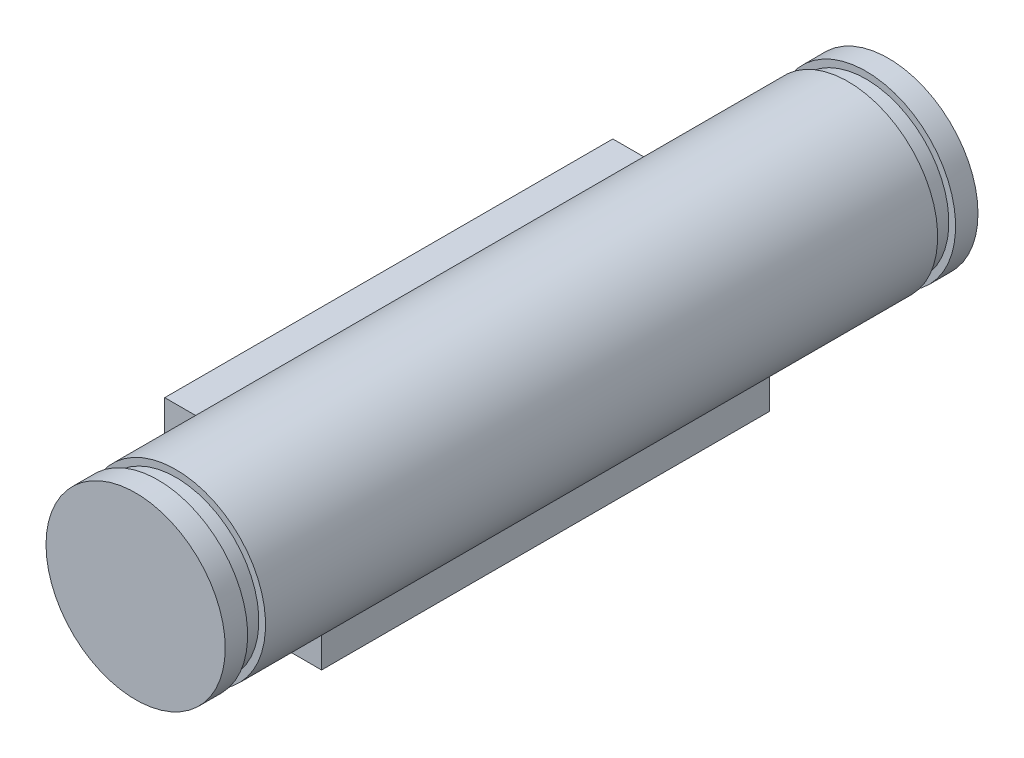
SolidWorks part; units mm, degrees
ref_plane "前视基准面" through (0, 0, 0) normal (0, 0, 1) x (1, 0, 0)
ref_plane "上视基准面" through (0, 0, 0) normal (0, 1, 0) x (1, 0, 0)
ref_plane "右视基准面" through (0, 0, 0) normal (1, 0, 0) x (0, 0, -1)
sketch "草图1" plane through (0, 0, 0) normal (0, 0, 1) x (1, 0, 0)
  line L0 (0, 7.5) -> (0, -7.5) construction
  line L1 (-7.5, -7.5) -> (7.5, -7.5)
  line L2 (-7.5, 7.5) -> (-7.5, -7.5)
  line L3 (-7.5, 7.5) -> (7.5, 7.5)
  line L4 (7.5, -7.5) -> (7.5, 7.5)
  line L5 (7.5, 0) -> (-7.5, 0) construction
  circle A0 centre (0, 0) radius 4
  circle A1 centre (-5, 5) radius 1.5
  circle A2 centre (-5, -5) radius 1.5
  circle A3 centre (5, -5) radius 1.5
  circle A4 centre (5, 5) radius 1.5
extrude "凸台-拉伸1" add sketch "草图1" along normal mid plane 33.6 contours A0
sketch "草图2" plane through (0, 0, 0) normal (1, 0, 0) x (0, 0, -1)
  line L0 (18.8, 0) -> (14.4802, 0) construction
  line L1 (-15, 3.7) -> (-15.8, 3.7)
  line L2 (-15, 4) -> (-15, 3.7)
  line L3 (-15.8, 3.7) -> (-15.8, 4)
  line L4 (-15.8, 4) -> (-15, 4)
  line L5 (0, 0) -> (0, 3) construction
  line L7 (15.8, 4) -> (15, 4)
  line L8 (15.8, 3.7) -> (15.8, 4)
  line L9 (15, 4) -> (15, 3.7)
  line L14 (15, 3.7) -> (15.8, 3.7)
revolve "切除-旋转1" cut sketch "草图2" angle 360 about L0
sketch "草图3" plane through (0, 0, 0) normal (0, 0, 1) x (-1, 0, 0)
  line L18 (5.5, 1.5) -> (3.7081, 1.5)
  line L19 (5.5, -1.53) -> (5.5, 1.5)
  line L20 (3.6958, -1.53) -> (5.5, -1.53)
  line L21 (-1.5, 5.5) -> (-1.5, 3.7081)
  line L22 (1.53, 5.5) -> (-1.5, 5.5)
  line L23 (1.53, 3.6958) -> (1.53, 5.5)
  arc A8 (3.7081, 1.5) -> (1.53, 3.6958) centre (0, 0) ccw
  arc A9 (-1.5, 3.7081) -> (3.6958, -1.53) centre (0, 0) ccw
extrude "凸台-拉伸2" add sketch "草图3" along normal mid plane 20
